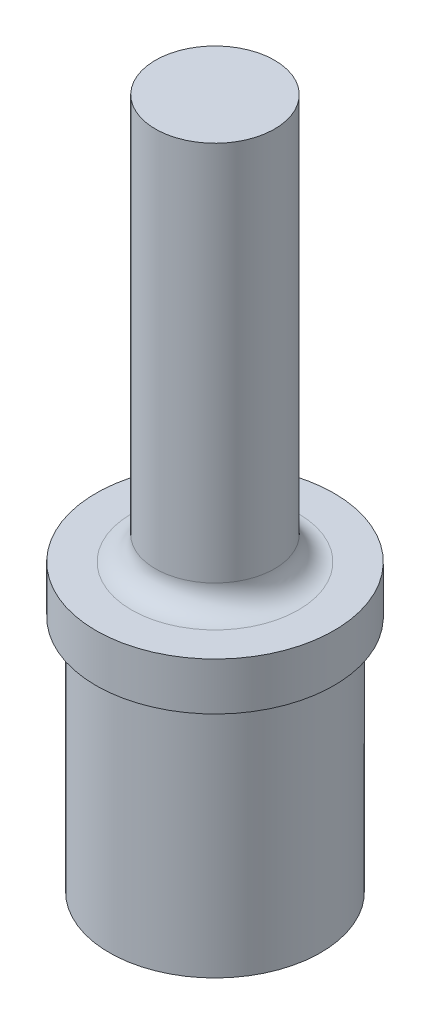
SolidWorks part; units mm, degrees
material "AISI 4130 Steel, normalized at 870C"
ref_plane "Front Plane" through (0, 0, 0) normal (0, 0, 1) x (1, 0, 0)
ref_plane "Top Plane" through (0, 0, 0) normal (0, 1, 0) x (1, 0, 0)
ref_plane "Right Plane" through (0, 0, 0) normal (1, 0, 0) x (0, 0, -1)
sketch "Sketch1" plane through (0, 0, 0) normal (0, 0, 1) x (1, 0, 0)
  line L0 (0, 0) -> (0, 13.2049) construction
  line L1 (0, 0) -> (-3.9751, 0)
  line L2 (-3.9751, 0) -> (-3.9751, -26.9875)
  line L3 (-3.9751, -26.9875) -> (-7.9375, -26.9875)
  line L4 (-7.9375, -26.9875) -> (-7.9375, -30.1625)
  line L5 (-7.9375, -30.1625) -> (-7.0485, -30.1625)
  line L6 (-7.0485, -30.1625) -> (-7.0485, -46.0375)
  line L7 (-7.0485, -46.0375) -> (-5.7785, -46.0375)
  line L8 (-5.7785, -46.0375) -> (-5.7785, -33.87)
  line L9 (-5.7785, -33.87) -> (0, -30.7975)
  line L10 (0, -30.7975) -> (0, 0)
  dimension "D1" = 7.9502
  dimension "D2" = 3.175
  dimension "D3" = 14.097
  dimension "D4" = 15.875
  dimension "D5" = 46.0375
  dimension "D6" = 1.27
  dimension "D7" = 26.9875
  dimension "D8" = 118
  dimension "D9" = 15.24
  dimension "D10" = 0.889
revolve "Revolve1" add sketch "Sketch1" angle 360 about L0
fillet "Fillet1" radius 1.5875 1 edges at (0, -26.9875, -3.9751)
